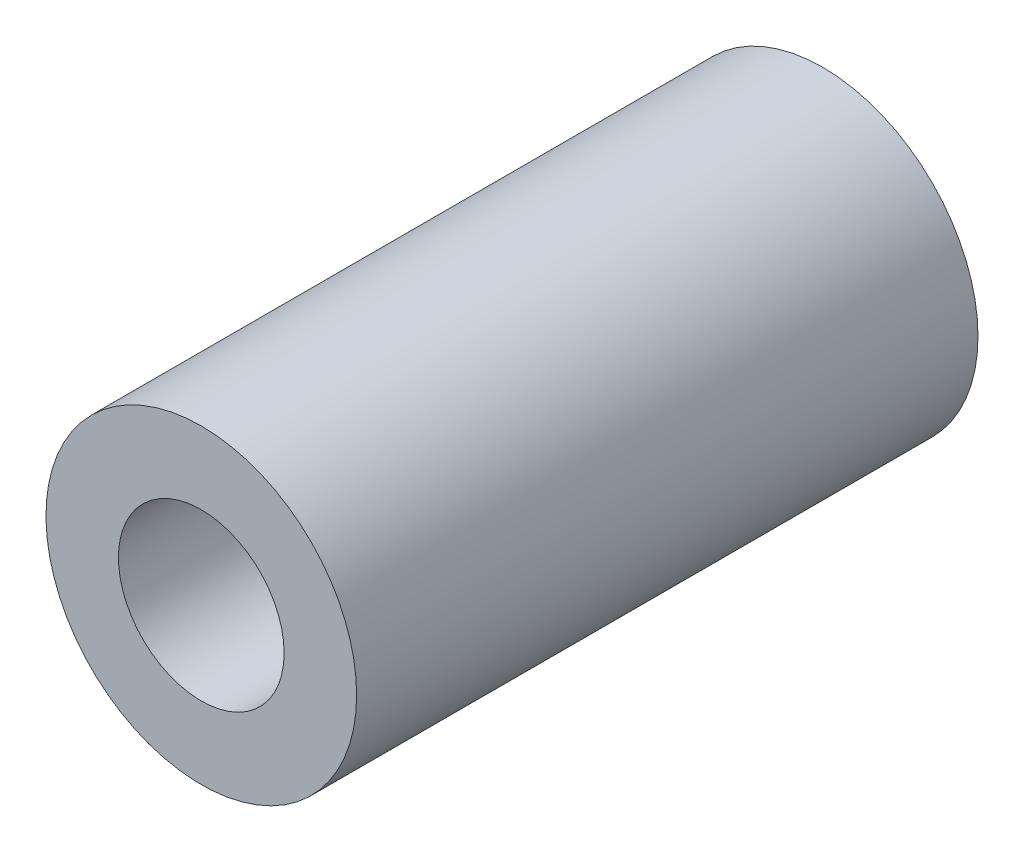
SolidWorks part; units mm, degrees
ref_plane "Front Plane" through (0, 0, 0) normal (0, 0, 1) x (1, 0, 0)
ref_plane "Top Plane" through (0, 0, 0) normal (0, 1, 0) x (1, 0, 0)
ref_plane "Right Plane" through (0, 0, 0) normal (1, 0, 0) x (0, 0, -1)
sketch "Sketch2" plane through (0, 0, 0) normal (0, 0, 1) x (1, 0, 0)
  line L0 (4, -96.0002) -> (9.6569, -90.3433) construction
  line L2 (1.3484, -93.3485) -> (7.0052, -87.6917)
  line L3 (6.6517, -98.6518) -> (12.3085, -92.995)
  arc A0 (1.3484, -93.3485) -> (6.6517, -98.6518) centre (4, -96.0002) ccw
  arc A1 (12.3085, -92.995) -> (7.0052, -87.6917) centre (9.6569, -90.3433) ccw
  circle A2 centre (9.6569, -90.3433) radius 2
  dimension "D3" = 7.5
  dimension "D4" = 4
  dimension "D2" = 8
extrude "Boss-Extrude1" add sketch "Sketch2" along normal blind 4
sketch "Sketch3" plane through (0, 0, 4) normal (0, 0, 1) x (1, 0, 0)
  circle A0 centre (4, -96.0002) radius 2
  dimension "D1" = 4
extrude "Cut-Extrude1" cut sketch "Sketch3" against normal blind 4
sketch "Sketch4" plane through (0, 0, 4) normal (0, 0, 1) x (1, 0, 0)
  circle A0 centre (4, -96.0002) radius 3
  dimension "D1" = 6
extrude "Cut-Extrude2" cut sketch "Sketch4" against normal blind 2
sketch "Sketch5" plane through (0, 0, 4) normal (0, 0, 1) x (1, 0, 0)
  circle A0 centre (9.6569, -90.3433) radius 3.75
  circle A1 centre (9.6569, -90.3433) radius 2
extrude "Boss-Extrude2" add sketch "Sketch5" along normal blind 11
